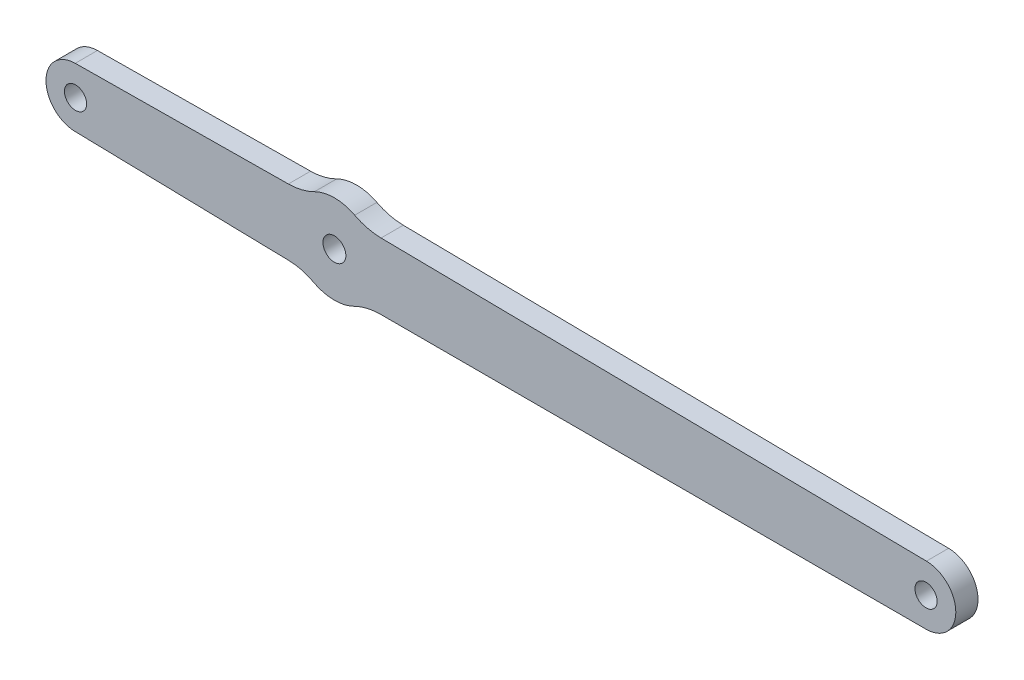
SolidWorks part; units mm, degrees
ref_plane "Front Plane" through (0, 0, 0) normal (0, 0, 1) x (1, 0, 0)
ref_plane "Top Plane" through (0, 0, 0) normal (0, 1, 0) x (1, 0, 0)
ref_plane "Right Plane" through (0, 0, 0) normal (1, 0, 0) x (0, 0, -1)
sketch "Model" plane through (0, 0, 0) normal (0, 0, 1) x (1, 0, 0)
  line L0 (32.9732, 21.048) -> (61.7836, 20.3966)
  line L1 (33.0253, 29.0468) -> (61.8417, 29.3229)
  line L2 (74.3745, 29.2627) -> (148.1136, 28.2974)
  line L3 (74.3161, 20.2934) -> (148.0615, 20.2978)
  arc A0 (33.0253, 29.0468) -> (32.9732, 21.048) centre (33.0636, 25.047) ccw
  arc A1 (65.2943, 19.4959) -> (61.7836, 20.3966) centre (61.719, 12.8521) ccw
  arc A2 (61.8417, 29.3229) -> (65.3638, 30.1776) centre (61.761, 37.3391) ccw
  circle A3 centre (68.0629, 24.819) radius 1.55
  arc A4 (65.2943, 19.4959) -> (70.7431, 19.4509) centre (68.0628, 24.819) ccw
  arc A5 (70.8127, 30.1517) -> (65.3638, 30.1776) centre (68.0628, 24.8194) ccw
  arc A6 (74.3161, 20.2934) -> (70.7431, 19.4509) centre (74.3167, 12.2928) ccw
  arc A7 (70.8127, 30.1517) -> (74.3745, 29.2627) centre (74.4794, 37.2627) ccw
  arc A8 (148.0615, 20.2978) -> (148.1136, 28.2974) centre (148.0875, 24.2976) ccw
  circle A9 centre (148.0612, 24.2978) radius 1.5
  circle A10 centre (33.0636, 25.047) radius 1.5
extrude "Boss-Extrude1" add sketch "Model" along normal blind 3
